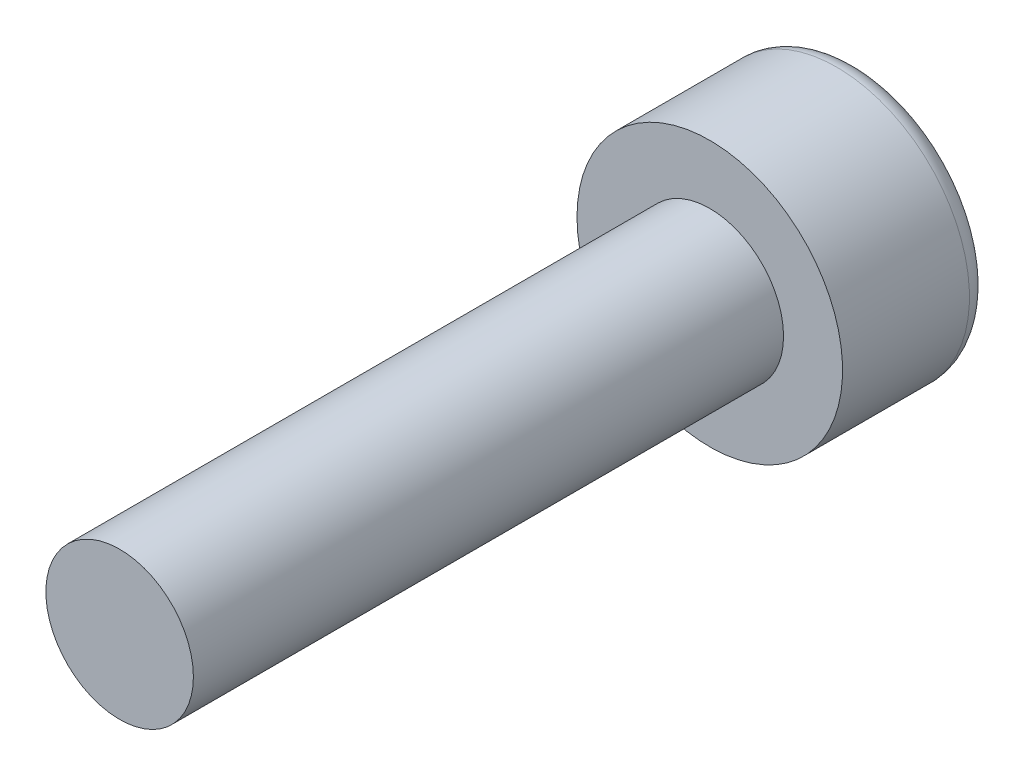
SolidWorks part; units mm, degrees
material "Acero aleado"
ref_plane "Alzado" through (0, 0, 0) normal (0, 0, 1) x (1, 0, 0)
ref_plane "Planta" through (0, 0, 0) normal (0, 1, 0) x (1, 0, 0)
ref_plane "Vista lateral" through (0, 0, 0) normal (1, 0, 0) x (0, 0, -1)
sketch "Croquis1" plane through (0, 0, 0) normal (0, 0, 1) x (1, 0, 0)
  circle A0 centre (0, 0) radius 1.25
  dimension "D1" = 2.5
extrude "Saliente-Extruir1" add sketch "Croquis1" along normal blind 10
sketch "Croquis2" plane through (0, 0, 0) normal (0, 0, -1) x (-1, 0, 0)
  circle A0 centre (0, 0) radius 2.25
  dimension "D1" = 4.5
extrude "Saliente-Extruir2" add sketch "Croquis2" along normal blind 2.5
sketch "Croquis3" plane through (0, 0, -2.5) normal (0, 0, -1) x (-1, 0, 0)
  line L1 (0, -1.1547) -> (1, -0.5774)
  line L2 (1, -0.5774) -> (1, 0.5774)
  line L3 (1, 0.5774) -> (0, 1.1547)
  line L4 (0, 1.1547) -> (-1, 0.5774)
  line L5 (-1, 0.5774) -> (-1, -0.5774)
  line L6 (-1, -0.5774) -> (0, -1.1547)
  circle A0 centre (0, 0) radius 1 construction
  dimension "D1" = 2
extrude "Cortar-Extruir1" cut sketch "Croquis3" against normal blind 1.5
fillet "Redondeo1" radius 0.35 1 edges at (-2.25, 0, -2.5)
